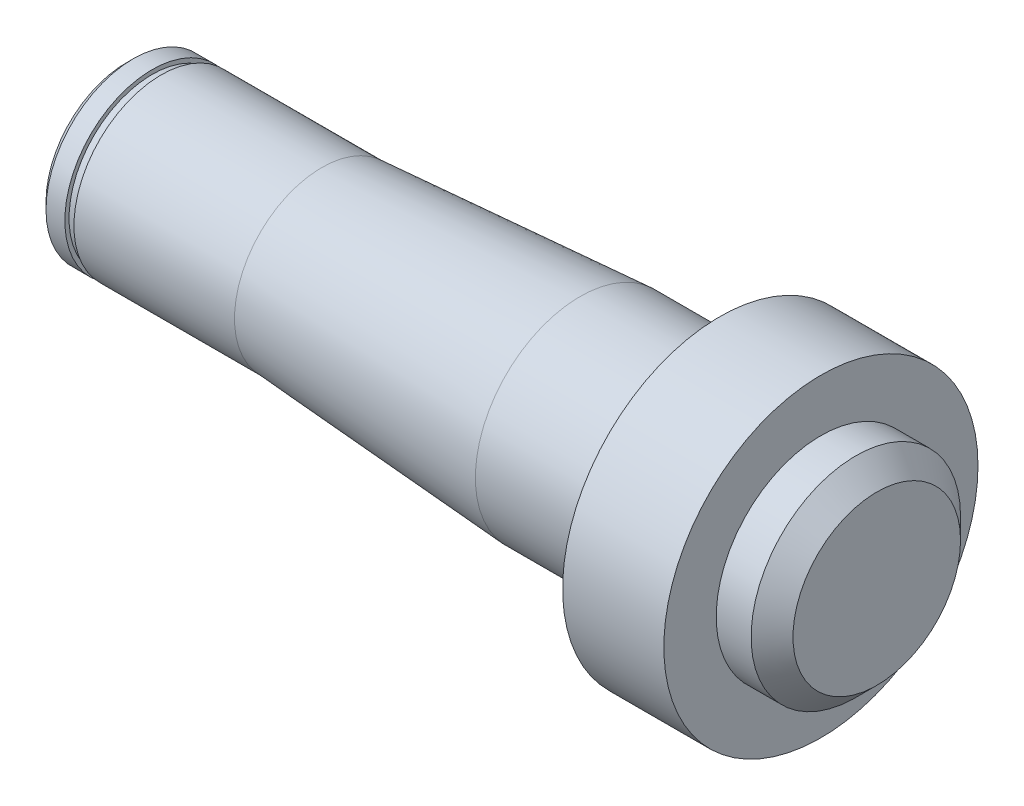
SolidWorks part; units mm, degrees
material "XC48"
ref_plane "Plan de face" through (0, 0, 0) normal (0, 0, 1) x (1, 0, 0)
ref_plane "Plan de dessus" through (0, 0, 0) normal (0, 1, 0) x (1, 0, 0)
ref_plane "Plan de droite" through (0, 0, 0) normal (1, 0, 0) x (0, 0, -1)
sketch "Esquisse1" plane through (0, 0, 0) normal (0, 0, 1) x (1, 0, 0)
  line L0 (0, 0) -> (-84.0824, 0) construction
  line L1 (0, 0) -> (0, 15)
  line L2 (0, 15) -> (-8, 15)
  line L3 (-8, 15) -> (-8, 22.5)
  line L4 (-8, 22.5) -> (-22.5, 22.5)
  line L5 (-22.5, 22.5) -> (-22.5, 15)
  line L6 (-22.5, 15) -> (-42.5, 15)
  line L7 (-42.5, 15) -> (-79.5, 12.5)
  line L8 (-79.5, 12.5) -> (-102.5, 12.5)
  line L9 (-102.5, 12.5) -> (-102.5, 11.9)
  line L10 (-102.5, 11.9) -> (-103.8, 11.9)
  line L11 (-103.8, 11.9) -> (-103.8, 12.5)
  line L12 (-103.8, 12.5) -> (-107.5, 12.5)
  line L13 (-107.5, 12.5) -> (-107.5, 0)
  line L14 (-107.5, 0) -> (0, 0)
  dimension "D1" = 30
  dimension "D2" = 45
  dimension "D3" = 30
  dimension "D4" = 25
  dimension "D5" = 23.8
  dimension "D6" = 1.3
  dimension "D7" = 107.5
  dimension "D8" = 57
  dimension "D9" = 14.5
  dimension "D10" = 8
  dimension "D11" = 20
  dimension "D12" = 80
revolve "Révolution1" add sketch "Esquisse1" angle 360 about L0
chamfer "Chanfrein1" distance 1 angle 45 1 edges at (-107.5, 0, -12.5)
chamfer "Chanfrein2" distance 3 angle 45 1 edges at (0, 0, -15)
